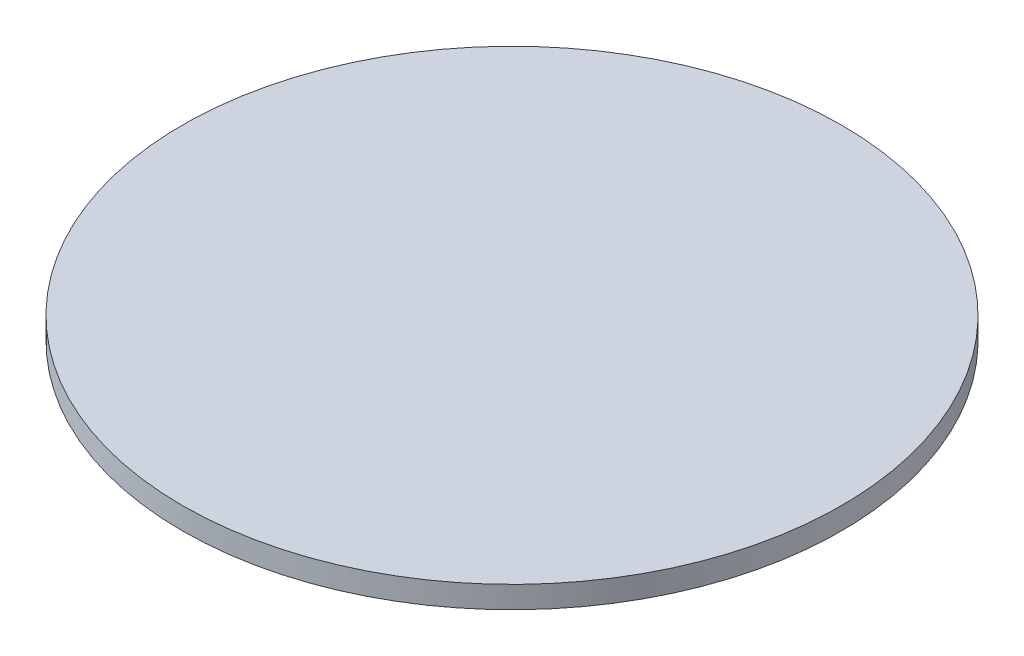
SolidWorks part; units mm, degrees
ref_plane "Front Plane" through (0, 0, 0) normal (0, 0, 1) x (1, 0, 0)
ref_plane "Top Plane" through (0, 0, 0) normal (0, 1, 0) x (1, 0, 0)
ref_plane "Right Plane" through (0, 0, 0) normal (1, 0, 0) x (0, 0, -1)
sketch "Sketch1" plane through (0, 0, 0) normal (0, 1, 0) x (1, 0, 0)
  circle A0 centre (0, 0) radius 1.5
  dimension "D1" = 3
extrude "Boss-Extrude1" add sketch "Sketch1" along normal blind 0.1
